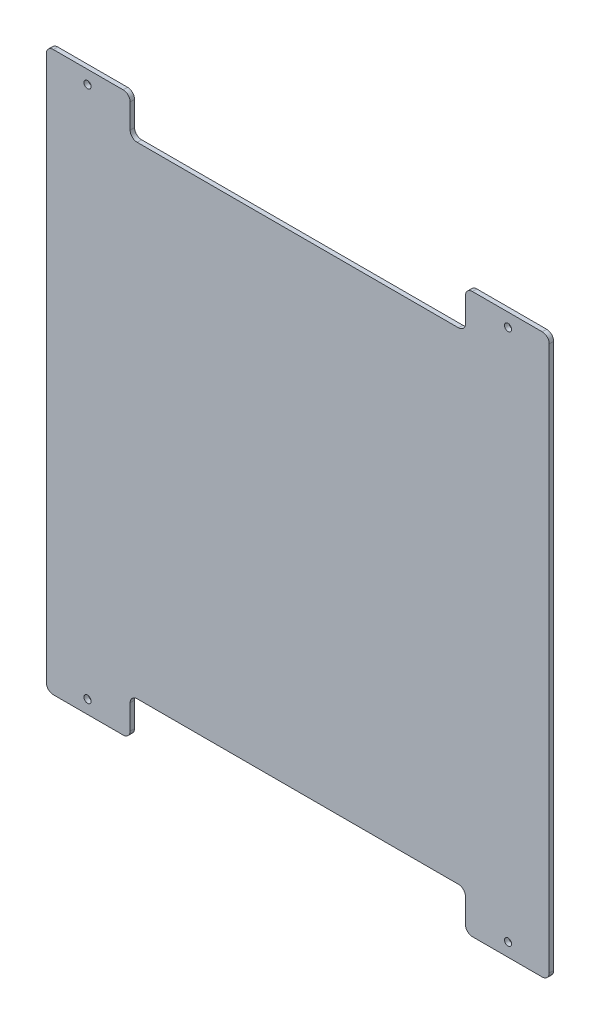
SolidWorks part; units mm, degrees
ref_plane "Front Plane" through (0, 0, 0) normal (0, 0, 1) x (1, 0, 0)
ref_plane "Top Plane" through (0, 0, 0) normal (0, 1, 0) x (1, 0, 0)
ref_plane "Right Plane" through (0, 0, 0) normal (1, 0, 0) x (0, 0, -1)
sketch "Model" plane through (0, 0, 0) normal (0, 0, 1) x (1, 0, 0)
  line L0 (175, 200) -> (125, 200)
  line L2 (-175, 200) -> (-125, 200)
  line L3 (-115, 172.5) -> (115, 172.5)
  line L4 (-120, 177.5) -> (-120, 195)
  line L7 (-180, -195) -> (-180, 195)
  line L8 (-120, -177.5) -> (-120, -195)
  line L9 (-175, -200) -> (-125, -200)
  line L10 (-115, -172.5) -> (115, -172.5)
  line L14 (180, 0) -> (-180, 0) construction
  line L15 (120, 177.5) -> (120, 195)
  line L16 (120, -177.5) -> (120, -195)
  line L17 (175, -200) -> (125, -200)
  line L18 (0, 172.5) -> (0, -172.5) construction
  line L23 (180, 195) -> (180, -195)
  arc A0 (120, -195) -> (125, -200) centre (125, -195) ccw
  arc A1 (175, -200) -> (180, -195) centre (175, -195) ccw
  arc A2 (180, 195) -> (175, 200) centre (175, 195) ccw
  arc A3 (120, 195) -> (125, 200) centre (125, 195) cw
  arc A4 (120, 177.5) -> (115, 172.5) centre (115, 177.5) cw
  arc A5 (-120, 177.5) -> (-115, 172.5) centre (-115, 177.5) ccw
  arc A6 (-125, -200) -> (-120, -195) centre (-125, -195) ccw
  arc A7 (-115, -172.5) -> (-120, -177.5) centre (-115, -177.5) ccw
  arc A8 (-180, -195) -> (-175, -200) centre (-175, -195) ccw
  arc A9 (-120, 195) -> (-125, 200) centre (-125, 195) ccw
  arc A10 (-175, 200) -> (-180, 195) centre (-175, 195) ccw
  arc A12 (120, -177.5) -> (115, -172.5) centre (115, -177.5) ccw
  dimension "D1" = 345
  dimension "D11" = 5
  dimension "D17" = 5
  dimension "D18" = 5
  dimension "D19" = 5
  dimension "D20" = 5
  dimension "D21" = 5
  dimension "D22" = 5
  dimension "D23" = 5
  dimension "D24" = 5
  dimension "D25" = 5
  dimension "D26" = 5
  dimension "D27" = 5
  dimension "D2" = 172.5
  dimension "D3" = 360
  dimension "D4" = 180
  dimension "D5" = 60
  dimension "D6" = 60
  dimension "D7" = 400
  dimension "D8" = 60
  dimension "D15" = 60
extrude "Boss-Extrude1" add sketch "Model" along normal blind 3.175
sketch "Sketch2" plane through (0, 0, 3.175) normal (0, 0, 1) x (1, 0, 0)
  line L0 (180, 0) -> (-180, 0) construction
  line L1 (180, 195) -> (180, -195) construction
  line L2 (-180, -195) -> (-180, 195) construction
  line L3 (0, 172.5) -> (0, -172.5) construction
  line L4 (-115, 172.5) -> (115, 172.5) construction
  line L5 (-115, -172.5) -> (115, -172.5) construction
  circle A0 centre (-150.5, 190.5) radius 2.55
  circle A1 centre (150.5, 190.5) radius 2.55
  circle A2 centre (150.5, -190.5) radius 2.55
  circle A3 centre (-150.5, -190.5) radius 2.55
  dimension "D1" = 5.1
  dimension "D3" = 150.5
  dimension "D4" = 190.5
  dimension "D5" = 150.5
  dimension "D6" = 190.5
  dimension "D7" = 150.5
  dimension "D8" = 190.5
  dimension "D9" = 150.5
  dimension "D2" = 190.5
extrude "Cut-Extrude1" cut sketch "Sketch2" against normal up to next contours A0 | A3 | A2 | A1
equation "\"D2@Model\"=\"D1@Model\"/2"
